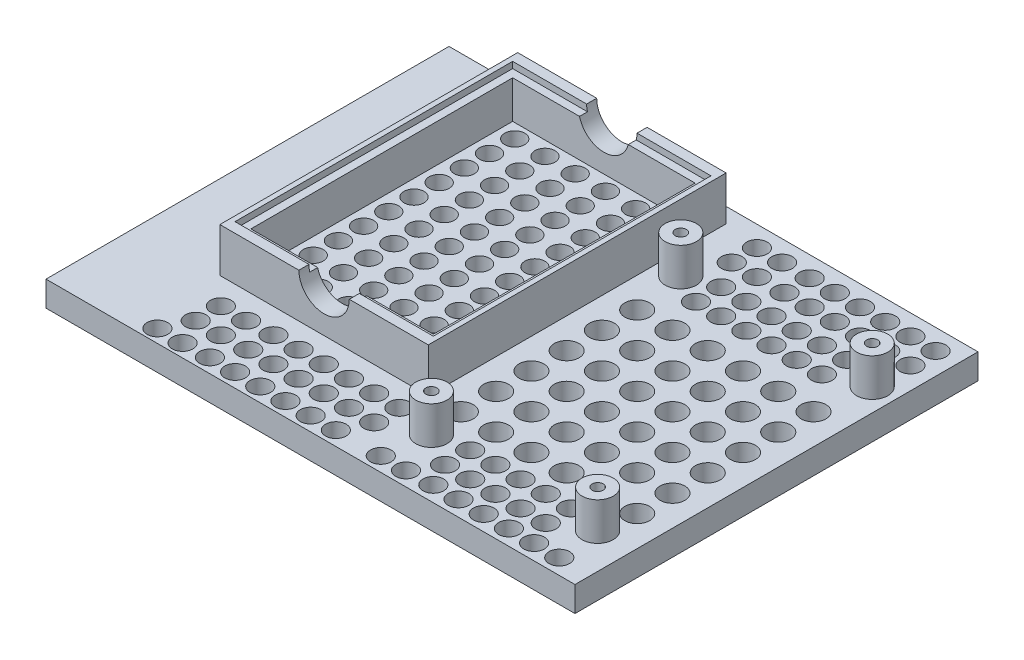
SolidWorks part; units mm, degrees
ref_plane "Front Plane" through (0, 0, 0) normal (0, 0, 1) x (1, 0, 0)
ref_plane "Top Plane" through (0, 0, 0) normal (0, 1, 0) x (1, 0, 0)
ref_plane "Right Plane" through (0, 0, 0) normal (1, 0, 0) x (0, 0, -1)
sketch "Sketch1" plane through (0, 0, 0) normal (0, 1, 0) x (1, 0, 0)
  circle A0 centre (0, 0) radius 41.275
  dimension "D1" = 82.55
extrude "Boss-Extrude1" add sketch "Sketch1" along normal blind 9.525
sketch "Sketch2" plane through (0, 0, 0) normal (0, -1, 0) x (1, 0, 0)
  line L1 (-25.4, 28.575) -> (25.4, 28.575)
  line L2 (-25.4, 28.575) -> (-25.4, 41.275)
  line L3 (-25.4, 41.275) -> (25.4, 41.275)
  line L4 (25.4, 28.575) -> (25.4, 41.275)
  line L5 (0, 41.275) -> (0, 28.575) construction
  line L6 (-25.4, 34.925) -> (25.4, 34.925) construction
  circle A0 centre (0, 0) radius 41.275 construction
  point P0 (0, 34.925)
  dimension "D1" = 12.7
  dimension "D2" = 50.8
extrude "Boss-Extrude2" add sketch "Sketch2" along normal blind 76.2
sketch "Sketch3" plane through (25.4, 0, 0) normal (1, 0, 0) x (0, 0, -1)
  line L0 (-41.275, 0) -> (-41.275, -76.2)
  line L1 (-41.275, -76.2) -> (-41.275, 0) construction
  line L2 (-41.275, -76.2) -> (-76.7393, -23.727)
  line L3 (-41.275, -76.2) -> (-28.575, -76.2) construction
  line L4 (-64.1375, 0) -> (-41.275, 0)
  line L6 (-41.275, 0) -> (-32.5341, 0) construction
  circle A0 centre (-64.1375, -15.21) radius 15.21 construction
  arc A1 (-64.1375, 0) -> (-76.7393, -23.727) centre (-64.1375, -15.21) ccw
  circle A2 centre (-64.1375, -15.21) radius 2.51
  dimension "D3" = 5.02
  dimension "D2" = 12.7
  dimension "D1" = 22.8625
extrude "Boss-Extrude3" add sketch "Sketch3" against normal blind 6.35
ref_plane "Plane1" through (7.4803, 0, 0) normal (-1, 0, 0) x (0, 0, 1)
ref_plane "Plane2" through (13.2651, 0, 0) normal (-1, 0, 0) x (0, 0, 1)
mirror "Mirror1" about plane through (13.2651, 0, 0) normal (-1, 0, 0) of "Boss-Extrude3"
sketch "Sketch5" plane through (1.1303, 0, 0) normal (-1, 0, 0) x (0, 0, 1)
  line L0 (42.9875, 0) -> (42.9875, 5.94)
  line L1 (42.9875, -36.36) -> (85.2875, -36.36) construction
  line L2 (42.9875, -36.36) -> (42.9875, 5.94) construction
  line L3 (42.9875, 5.94) -> (85.2875, 5.94) construction
  line L4 (85.2875, -36.36) -> (85.2875, 5.94) construction
  line L5 (64.1375, 5.94) -> (64.1375, -36.36) construction
  line L6 (42.9875, -15.21) -> (85.2875, -15.21) construction
  line L7 (41.275, 0) -> (64.1375, 0) construction
  line L8 (42.9875, 5.94) -> (85.2875, 5.94)
  line L9 (85.2875, 5.94) -> (85.2875, -36.36)
  line L10 (85.2875, -36.36) -> (68.2012, -36.36)
  line L11 (76.7393, -23.727) -> (41.275, -76.2) construction
  line L12 (64.1375, 0) -> (42.9875, 0)
  line L13 (76.7393, -23.727) -> (68.2012, -36.36)
  arc A0 (64.1375, 0) -> (76.7393, -23.727) centre (64.1375, -15.21) cw
  arc A1 (76.7393, -23.727) -> (64.1375, 0) centre (64.1375, -15.21) ccw construction
  point P0 (64.1375, -15.21)
  dimension "D1" = 42.3
extrude "Boss-Extrude4" add sketch "Sketch5" against normal up to surface (6.35 mm away) up to face at (7.4803, -24.0348, 57.6397)
sketch "Sketch6" plane through (1.1303, 0, 0) normal (-1, 0, 0) x (0, 0, 1)
  line L1 (48.6375, -30.71) -> (79.6375, -30.71) construction
  line L2 (48.6375, -30.71) -> (48.6375, 0.29) construction
  line L3 (48.6375, 0.29) -> (79.6375, 0.29) construction
  line L4 (79.6375, -30.71) -> (79.6375, 0.29) construction
  line L5 (64.1375, 0.29) -> (64.1375, -30.71) construction
  line L6 (48.6375, -15.21) -> (79.6375, -15.21) construction
  circle A0 centre (48.6375, 0.29) radius 2
  circle A1 centre (79.6375, 0.29) radius 2
  circle A2 centre (79.6375, -30.71) radius 2
  circle A3 centre (48.6375, -30.71) radius 2
  point P0 (64.1375, -15.21)
  dimension "D2" = 4
  dimension "D1" = 31
extrude "Cut-Extrude1" cut sketch "Sketch6" against normal through all
sketch "Sketch7" plane through (1.1303, 0, 0) normal (-1, 0, 0) x (0, 0, 1)
  circle A0 centre (64.1375, -15.21) radius 10.9995
  dimension "D1" = 21.9989
extrude "Cut-Extrude2" cut sketch "Sketch7" against normal blind 2.0015
sketch "Sketch8" plane through (25.4, 0, 0) normal (-1, 0, 0) x (0, 0, 1)
  line L1 (55.1485, -74.46) -> (61.7525, -74.46)
  line L2 (55.1485, -74.46) -> (55.1485, -36.36)
  line L3 (55.1485, -36.36) -> (61.7525, -36.36)
  line L4 (61.7525, -74.46) -> (61.7525, -36.36)
  line L5 (58.4505, -36.36) -> (58.4505, -74.46) construction
  line L6 (55.1485, -55.41) -> (61.7525, -55.41) construction
  line L7 (68.2012, -36.36) -> (85.2875, -36.36) construction
  line L8 (41.275, -76.2) -> (41.275, 0) construction
  point P220 (58.4505, -55.41)
  dimension "D1" = 13.8735
  dimension "D2" = 6.604
  dimension "D3" = 38.1
extrude "Boss-Extrude5" add sketch "Sketch8" along normal up to surface (24.2697 mm away)
sketch "Sketch9" plane through (0, 9.525, 0) normal (0, 1, 0) x (1, 0, 0)
  line L1 (17.6771, -17.6771) -> (-17.6771, -17.6771) construction
  line L2 (17.6771, -17.6771) -> (17.6771, 17.6771) construction
  line L3 (17.6771, 17.6771) -> (-17.6771, 17.6771) construction
  line L4 (-17.6771, -17.6771) -> (-17.6771, 17.6771) construction
  line L5 (0, 17.6771) -> (0, -17.6771) construction
  line L6 (17.6771, 0) -> (-17.6771, 0) construction
  circle A0 centre (-17.6771, -17.6771) radius 2.5006
  circle A1 centre (17.6771, -17.6771) radius 2.5006
  circle A2 centre (17.6771, 17.6771) radius 2.5006
  circle A3 centre (-17.6771, 17.6771) radius 2.5006
  point P0 (0, 0)
  dimension "D2" = 5.0013
  dimension "D1" = 35.3543
extrude "Cut-Extrude3" cut sketch "Sketch9" against normal through all
sketch "Sketch11" plane through (0, 0, 0) normal (1, 0, 0) x (0, 0, -1)
  line L0 (34.925, 0) -> (-28.575, -76.2)
  line L1 (-32.5341, 0) -> (41.275, 0) construction
  dimension "D1" = 6.35
rib "Rib2" sketch "Sketch11" sketch "Sketch11" thickness 12.7 extrusion direction parallel to sketch draft on no parameters "D1"=12.7
fillet "Fillet2" radius 6.35 3 edges at (-6.35, -38.1, 28.575) (6.35, -38.1, 28.575) (0, 0, -41.275)
fillet "Fillet3" radius 6.35 6 edges at (-19.05, -76.2, 28.575) (-8.2099, -73.9682, 26.7151) (19.05, -76.2, 28.575) (8.2099, -73.9682, 26.7151) (-6.35, -34.276, -6.3617) (6.35, -34.276, -6.3617)
fillet "Fillet4" radius 6.35 9 edges at (-6.6806, -73.6896, 26.9338) (6.6687, -73.7059, 26.9387) (0, -76.2, 28.575) (-25.4, -76.2, 38.1) (-25.4, -74.3401, 30.4349) (25.4, -76.2, 38.1) (25.4, -74.3401, 30.4349) (-25.4, -34.4604, 28.575) (25.4, -34.4604, 28.575)
fillet "Fillet5" radius 2.032 12 edges at (4.3053, -45.9015, 61.7525) (22.225, -45.9015, 61.7525) (1.1303, -74.46, 58.4505) (13.2651, -74.46, 55.1485) (25.4, -74.46, 58.4505) (0.5651, 0, 41.275) (1.1303, 0, 42.1313) (4.3053, 5.94, 85.2875) (4.3053, -36.36, 85.2875) (4.3053, -36.36, 68.2012) (4.3053, 0, 42.9875) (4.3053, 5.94, 42.9875)
sketch "Sketch12" plane through (0, 0, 0) normal (0, 1, 0) x (1, 0, 0)
  line L0 (25.4, -34.925) -> (25.4, -46.6587) construction
  line L1 (25.4, -32.5341) -> (158.75, -32.5341)
  line L2 (25.4, -32.5341) -> (25.4, 69.0659)
  line L3 (25.4, 69.0659) -> (158.75, 69.0659)
  line L4 (158.75, -32.5341) -> (158.75, 69.0659)
  line L5 (92.075, 69.0659) -> (92.075, -32.5341) construction
  line L6 (25.4, 18.2659) -> (158.75, 18.2659) construction
  circle A0 centre (0, 0) radius 41.275 construction
  point P288 (92.075, 18.2659)
  dimension "D1" = 101.6
  dimension "D2" = 133.35
extrude "Boss-Extrude6" add sketch "Sketch12" against normal blind 6.35
sketch "Sketch13" plane through (0, 0, 0) normal (0, 1, 0) x (1, 0, 0)
  line L0 (158.75, -32.5341) -> (158.75, 69.0659) construction
  line L1 (156.21, -26.1841) -> (156.21, 62.7159) construction
  line L2 (156.21, -26.1841) -> (101.6, -26.1841) construction
  line L3 (101.6, -26.1841) -> (101.6, 62.7159) construction
  line L4 (156.21, 62.7159) -> (101.6, 62.7159) construction
  line L5 (101.6, 18.2659) -> (156.21, 18.2659) construction
  line L6 (128.905, -26.1841) -> (128.905, 62.7159) construction
  line L7 (47.79, -7.2841) -> (97.79, -7.2841)
  line L8 (47.79, -7.2841) -> (47.79, 62.7159)
  line L9 (47.79, 62.7159) -> (97.79, 62.7159)
  line L10 (97.79, -7.2841) -> (97.79, 62.7159)
  line L11 (72.79, 62.7159) -> (72.79, -7.2841) construction
  line L12 (47.79, 27.7159) -> (97.79, 27.7159) construction
  line L13 (25.4, -32.5341) -> (158.75, -32.5341) construction
  line L15 (95.79, -5.2841) -> (49.79, -5.2841)
  line L16 (95.79, -5.2841) -> (95.79, 60.7159)
  line L17 (95.79, 60.7159) -> (49.79, 60.7159)
  line L18 (49.79, -5.2841) -> (49.79, 60.7159)
  line L19 (72.79, 60.7159) -> (72.79, -5.2841) construction
  line L20 (95.79, 27.7159) -> (49.79, 27.7159) construction
  circle A0 centre (107.95, -17.9291) radius 1.397
  circle A1 centre (104.775, 48.1109) radius 1.397
  circle A2 centre (0, 0) radius 41.275 construction
  circle A3 centre (149.86, -17.9291) radius 1.397
  circle A4 centre (153.035, 48.1109) radius 1.397
  circle A5 centre (0, 0) radius 41.275 construction
  circle A6 centre (104.775, 48.1109) radius 3.937
  circle A7 centre (153.035, 48.1109) radius 3.937
  circle A8 centre (107.95, -17.9291) radius 3.937
  circle A9 centre (149.86, -17.9291) radius 3.937
  point P0 (128.905, 18.2659)
  point P5 (72.79, 27.7159)
  point P20 (72.79, 27.7159)
  dimension "D5" = 6.35
  dimension "D6" = 8.255
  dimension "D7" = 3.175
  dimension "D8" = 14.605
  dimension "D9" = 2.794
  dimension "D15" = 2.54
  dimension "D1" = 54.61
  dimension "D2" = 88.9
  dimension "D3" = 50
  dimension "D4" = 70
  dimension "D10" = 2.54
  dimension "D11" = 50.8
  dimension "D12" = 3.81
  dimension "D13" = 2
  dimension "D14" = 2
extrude "Boss-Extrude7" add sketch "Sketch13" along normal blind 9.525
sketch "Sketch14" plane through (0, 0, 0) normal (0, 1, 0) x (1, 0, 0)
  line L0 (97.79, 62.7159) -> (47.79, 62.7159) construction
  line L1 (46.52, 65.2559) -> (99.06, 65.2559)
  line L2 (46.52, 65.2559) -> (46.52, -9.8241)
  line L3 (46.52, -9.8241) -> (99.06, -9.8241)
  line L4 (99.06, 65.2559) -> (99.06, -9.8241)
  line L5 (72.79, -9.8241) -> (72.79, 65.2559) construction
  line L6 (46.52, 27.7159) -> (99.06, 27.7159) construction
  line L7 (97.79, -7.2841) -> (97.79, 62.7159) construction
  line L8 (97.79, 62.7159) -> (47.79, 62.7159) construction
  line L9 (47.79, 62.7159) -> (47.79, -7.2841) construction
  line L11 (47.79, 62.7159) -> (97.79, 62.7159)
  line L12 (47.79, 62.7159) -> (47.79, -7.2841)
  line L13 (47.79, -7.2841) -> (97.79, -7.2841)
  line L14 (97.79, 62.7159) -> (97.79, -7.2841)
  line L15 (72.79, -7.2841) -> (72.79, 62.7159) construction
  line L16 (47.79, 27.7159) -> (97.79, 27.7159) construction
  point P8 (72.79, 62.7159)
  point P12 (47.79, 27.7159)
  point P200 (72.79, 27.7159)
  point P423 (72.79, 27.7159)
  dimension "D1" = 2.54
  dimension "D2" = 1.27
extrude "Boss-Extrude8" add sketch "Sketch14" along normal offset from surface (11.1125 mm away) 1.5875
sketch "Sketch15" plane through (0, 0, 9.8241) normal (0, 0, 1) x (1, 0, 0)
  line L0 (99.06, 11.1125) -> (46.52, 11.1125) construction
  line L1 (66.44, 11.1125) -> (79.14, 11.1125)
  arc A0 (66.44, 11.1125) -> (79.14, 11.1125) centre (72.79, 11.1125) ccw
  dimension "D1" = 12.7
extrude "Cut-Extrude4" cut sketch "Sketch15" against normal through all
sketch "Sketch16" plane through (0, 9.525, 0) normal (0, 1, 0) x (1, 0, 0)
  circle A0 centre (0, 0) radius 41.275
  circle A1 centre (-17.6771, 17.6771) radius 2.5006
  circle A2 centre (17.6771, 17.6771) radius 2.5006
  circle A3 centre (17.6771, -17.6771) radius 2.5006
  circle A4 centre (-17.6771, -17.6771) radius 2.5006
  circle A5 centre (0, 0) radius 41.275 construction
  circle A6 centre (-17.6771, -17.6771) radius 2.5006 construction
extrude "Boss-Extrude9" add sketch "Sketch16" along normal up to surface (1.5875 mm away)
sketch "Sketch17" plane through (7.4803, 0, 0) normal (1, 0, 0) x (0, 0, -1)
  circle A0 centre (-48.6375, 0.29) radius 2.9997
  circle A1 centre (-79.6375, 0.29) radius 2.9997
  circle A2 centre (-48.6375, -30.71) radius 2.9997
  circle A3 centre (-79.1747, -30.9662) radius 2.9997
  dimension "D1" = 5.9995
extrude "Cut-Extrude5" cut sketch "Sketch17" against normal blind 4.0005
sketch "Sketch18" plane through (1.1303, 0, 0) normal (-1, 0, 0) x (0, 0, 1)
  line L0 (83.2555, 5.94) -> (45.0195, 5.94) construction
  line L1 (83.2555, -36.36) -> (45.0195, -36.36)
  line L2 (85.2875, -34.328) -> (85.2875, 3.908)
  line L3 (83.2555, 5.94) -> (45.0195, 5.94)
  line L4 (42.9875, -34.328) -> (42.9875, 3.908)
  line L5 (64.1375, 5.94) -> (64.1375, -36.36) construction
  line L6 (85.2875, -15.21) -> (42.9875, -15.21) construction
  line L7 (42.9875, 3.908) -> (42.9875, 2.032) construction
  arc A0 (45.0195, -36.36) -> (42.9875, -34.328) centre (45.0195, -34.328) cw
  arc A1 (83.2555, -36.36) -> (85.2875, -34.328) centre (83.2555, -34.328) ccw
  arc A2 (85.2875, 3.908) -> (83.2555, 5.94) centre (83.2555, 3.908) ccw
  arc A3 (45.0195, 5.94) -> (42.9875, 3.908) centre (45.0195, 3.908) ccw
  circle A4 centre (48.6375, 0.29) radius 2
  circle A5 centre (48.6375, 0.29) radius 2 construction
  circle A6 centre (48.6375, -30.71) radius 2
  circle A7 centre (79.6375, 0.29) radius 2
  circle A8 centre (79.6375, -30.71) radius 2
  circle A9 centre (64.1375, -15.21) radius 10.9995
  circle A10 centre (64.1375, -15.21) radius 10.9995 construction
  point P0 (64.1375, -15.21)
  dimension "D1" = 2.032
extrude "Boss-Extrude10" add sketch "Sketch18" along normal blind 2.6492
sketch "Sketch19" plane through (0, 0, -69.0659) normal (0, 0, -1) x (-1, 0, 0)
  line L0 (-41.275, 11.1125) -> (-41.275, 0)
  line L1 (-158.75, 0) -> (-25.4, 0) construction
  line L2 (-41.275, 0) -> (-25.4, 0)
  line L3 (-25.4, -6.35) -> (-25.4, 0) construction
  line L4 (-25.4, 0) -> (-25.4, -76.2)
  line L5 (-25.4, -76.2) -> (25.9886, -76.2)
  line L6 (25.9886, -76.2) -> (25.9886, 0)
  line L8 (25.9886, 0) -> (41.275, 0)
  line L9 (41.275, 0) -> (41.275, 11.1125)
  line L10 (41.275, 11.1125) -> (-41.275, 11.1125)
  line L11 (4.0774, -76.2) -> (-4.0774, -76.2) construction
  line L12 (0, 0) -> (34.925, 0) construction
extrude "Cut-Extrude6" cut sketch "Sketch19" against normal through all
sketch "Sketch20" plane through (0, 0, 0) normal (0, 1, 0) x (1, 0, 0)
  line L0 (95.79, -5.2841) -> (95.79, 60.7159) construction
  line L1 (158.75, -32.5341) -> (158.75, 69.0659) construction
  line L2 (158.75, 18.2659) -> (25.4, 18.2659) construction
  line L3 (25.4, 69.0659) -> (25.4, -32.5341) construction
  circle A0 centre (91.98, 0) radius 2.5244
  circle A1 centre (84.36, 0) radius 2.5244
  circle A2 centre (76.74, 0) radius 2.5244
  circle A3 centre (69.12, 0) radius 2.5244
  circle A4 centre (61.5, 0) radius 2.5244
  circle A5 centre (53.88, 0) radius 2.5244
  circle A6 centre (91.98, 6.35) radius 2.5244
  circle A7 centre (84.36, 6.35) radius 2.5244
  circle A8 centre (53.88, 6.35) radius 2.5244
  circle A9 centre (69.12, 6.35) radius 2.5244
  circle A10 centre (76.74, 6.35) radius 2.5244
  circle A11 centre (61.5, 6.35) radius 2.5244
  circle A12 centre (91.98, 12.7) radius 2.5244
  circle A13 centre (84.36, 12.7) radius 2.5244
  circle A14 centre (53.88, 12.7) radius 2.5244
  circle A15 centre (69.12, 12.7) radius 2.5244
  circle A16 centre (76.74, 12.7) radius 2.5244
  circle A17 centre (61.5, 12.7) radius 2.5244
  circle A18 centre (91.98, 19.05) radius 2.5244
  circle A19 centre (84.36, 19.05) radius 2.5244
  circle A20 centre (53.88, 19.05) radius 2.5244
  circle A21 centre (69.12, 19.05) radius 2.5244
  circle A22 centre (76.74, 19.05) radius 2.5244
  circle A23 centre (61.5, 19.05) radius 2.5244
  circle A24 centre (91.98, 25.4) radius 2.5244
  circle A25 centre (84.36, 25.4) radius 2.5244
  circle A26 centre (53.88, 25.4) radius 2.5244
  circle A27 centre (69.12, 25.4) radius 2.5244
  circle A28 centre (76.74, 25.4) radius 2.5244
  circle A29 centre (61.5, 25.4) radius 2.5244
  circle A30 centre (91.98, 31.75) radius 2.5244
  circle A31 centre (84.36, 31.75) radius 2.5244
  circle A32 centre (53.88, 31.75) radius 2.5244
  circle A33 centre (69.12, 31.75) radius 2.5244
  circle A34 centre (76.74, 31.75) radius 2.5244
  circle A35 centre (61.5, 31.75) radius 2.5244
  circle A36 centre (91.98, 38.1) radius 2.5244
  circle A37 centre (84.36, 38.1) radius 2.5244
  circle A38 centre (53.88, 38.1) radius 2.5244
  circle A39 centre (69.12, 38.1) radius 2.5244
  circle A40 centre (76.74, 38.1) radius 2.5244
  circle A41 centre (61.5, 38.1) radius 2.5244
  circle A42 centre (91.98, 44.45) radius 2.5244
  circle A43 centre (84.36, 44.45) radius 2.5244
  circle A44 centre (53.88, 44.45) radius 2.5244
  circle A45 centre (69.12, 44.45) radius 2.5244
  circle A46 centre (76.74, 44.45) radius 2.5244
  circle A47 centre (61.5, 44.45) radius 2.5244
  circle A48 centre (91.98, 50.8) radius 2.5244
  circle A49 centre (84.36, 50.8) radius 2.5244
  circle A50 centre (53.88, 50.8) radius 2.5244
  circle A51 centre (69.12, 50.8) radius 2.5244
  circle A52 centre (76.74, 50.8) radius 2.5244
  circle A53 centre (61.5, 50.8) radius 2.5244
  circle A54 centre (91.98, 57.15) radius 2.5244
  circle A55 centre (84.36, 57.15) radius 2.5244
  circle A56 centre (53.88, 57.15) radius 2.5244
  circle A57 centre (69.12, 57.15) radius 2.5244
  circle A58 centre (76.74, 57.15) radius 2.5244
  circle A59 centre (61.5, 57.15) radius 2.5244
  circle A60 centre (151.1007, -9.1992) radius 3.1326
  circle A61 centre (141.6398, -16.4383) radius 2.6018
  circle A62 centre (144.018, 50.8) radius 2.6018
  circle A63 centre (137.668, 50.8) radius 2.6018
  circle A64 centre (131.318, 50.8) radius 2.6018
  circle A65 centre (124.968, 50.8) radius 2.6018
  circle A66 centre (118.618, 50.8) radius 2.6018
  circle A67 centre (112.268, 50.8) radius 2.6018
  circle A68 centre (137.668, 44.45) radius 2.6018
  circle A69 centre (131.318, 44.45) radius 2.6018
  circle A70 centre (124.968, 44.45) radius 2.6018
  circle A71 centre (118.618, 44.45) radius 2.6018
  circle A72 centre (112.268, 44.45) radius 2.6018
  circle A73 centre (144.018, 44.45) radius 2.6018
  circle A74 centre (142.2107, -9.1992) radius 3.1326
  circle A75 centre (133.3207, -9.1992) radius 3.1326
  circle A76 centre (124.4307, -9.1992) radius 3.1326
  circle A77 centre (115.5407, -9.1992) radius 3.1326
  circle A78 centre (106.6507, -9.1992) radius 3.1326
  circle A79 centre (142.2107, -0.3092) radius 3.1326
  circle A80 centre (133.3207, -0.3092) radius 3.1326
  circle A81 centre (124.4307, -0.3092) radius 3.1326
  circle A82 centre (115.5407, -0.3092) radius 3.1326
  circle A83 centre (106.6507, -0.3092) radius 3.1326
  circle A84 centre (142.2107, 8.5808) radius 3.1326
  circle A85 centre (133.3207, 8.5808) radius 3.1326
  circle A86 centre (124.4307, 8.5808) radius 3.1326
  circle A87 centre (115.5407, 8.5808) radius 3.1326
  circle A88 centre (106.6507, 8.5808) radius 3.1326
  circle A89 centre (142.2107, 17.4708) radius 3.1326
  circle A90 centre (133.3207, 17.4708) radius 3.1326
  circle A91 centre (124.4307, 17.4708) radius 3.1326
  circle A92 centre (115.5407, 17.4708) radius 3.1326
  circle A93 centre (106.6507, 17.4708) radius 3.1326
  circle A94 centre (142.2107, 26.3608) radius 3.1326
  circle A95 centre (133.3207, 26.3608) radius 3.1326
  circle A96 centre (124.4307, 26.3608) radius 3.1326
  circle A97 centre (115.5407, 26.3608) radius 3.1326
  circle A98 centre (106.6507, 26.3608) radius 3.1326
  circle A99 centre (142.2107, 35.2508) radius 3.1326
  circle A100 centre (133.3207, 35.2508) radius 3.1326
  circle A101 centre (124.4307, 35.2508) radius 3.1326
  circle A102 centre (115.5407, 35.2508) radius 3.1326
  circle A103 centre (106.6507, 35.2508) radius 3.1326
  circle A104 centre (151.1007, -0.3092) radius 3.1326
  circle A105 centre (151.1007, 8.5808) radius 3.1326
  circle A106 centre (151.1007, 17.4708) radius 3.1326
  circle A107 centre (151.1007, 26.3608) radius 3.1326
  circle A108 centre (151.1007, 35.2508) radius 3.1326
  circle A109 centre (135.2898, -16.4383) radius 2.6018
  circle A110 centre (128.9398, -16.4383) radius 2.6018
  circle A111 centre (122.5898, -16.4383) radius 2.6018
  circle A112 centre (116.2398, -16.4383) radius 2.6018
  circle A113 centre (153.2189, 63.9054) radius 2.6018
  circle A114 centre (135.2898, -22.7883) radius 2.6018
  circle A115 centre (128.9398, -22.7883) radius 2.6018
  circle A116 centre (122.5898, -22.7883) radius 2.6018
  circle A117 centre (116.2398, -22.7883) radius 2.6018
  circle A118 centre (146.8689, 63.9054) radius 2.6018
  circle A119 centre (141.6398, -22.7883) radius 2.6018
  circle A120 centre (140.5189, 63.9054) radius 2.6018
  circle A121 centre (134.1689, 63.9054) radius 2.6018
  circle A122 centre (127.8189, 63.9054) radius 2.6018
  circle A123 centre (121.4689, 63.9054) radius 2.6018
  circle A124 centre (146.8689, 57.5554) radius 2.6018
  circle A125 centre (140.5189, 57.5554) radius 2.6018
  circle A126 centre (134.1689, 57.5554) radius 2.6018
  circle A127 centre (127.8189, 57.5554) radius 2.6018
  circle A128 centre (121.4689, 57.5554) radius 2.6018
  circle A129 centre (153.2189, 57.5554) radius 2.6018
  circle A130 centre (114.5686, 63.8666) radius 2.6018
  circle A131 centre (108.2186, 63.8666) radius 2.6018
  circle A132 centre (98.0525, -16.1079) radius 2.6018
  circle A133 centre (91.7025, -16.1079) radius 2.6018
  circle A134 centre (85.3525, -16.1079) radius 2.6018
  circle A135 centre (79.0025, -16.1079) radius 2.6018
  circle A136 centre (108.2186, 57.5166) radius 2.6018
  circle A137 centre (72.6525, -16.1079) radius 2.6018
  circle A138 centre (66.3025, -16.1079) radius 2.6018
  circle A139 centre (91.7025, -22.4579) radius 2.6018
  circle A140 centre (85.3525, -22.4579) radius 2.6018
  circle A141 centre (114.5686, 57.5166) radius 2.6018
  circle A142 centre (79.0025, -22.4579) radius 2.6018
  circle A143 centre (72.6525, -22.4579) radius 2.6018
  circle A144 centre (66.3025, -22.4579) radius 2.6018
  circle A145 centre (98.0525, -22.4579) radius 2.6018
  circle A146 centre (59.7081, -16.4043) radius 2.6018
  circle A147 centre (53.3581, -16.4043) radius 2.6018
  circle A148 centre (144.544, -28.6379) radius 2.6018
  circle A149 centre (138.194, -28.6379) radius 2.6018
  circle A150 centre (131.844, -28.6379) radius 2.6018
  circle A151 centre (125.494, -28.6379) radius 2.6018
  circle A152 centre (53.3581, -22.7543) radius 2.6018
  circle A153 centre (119.144, -28.6379) radius 2.6018
  circle A154 centre (150.894, -28.6379) radius 2.6018
  circle A155 centre (106.1996, -28.9343) radius 2.6018
  circle A156 centre (112.5496, -28.9343) radius 2.6018
  circle A157 centre (59.7081, -22.7543) radius 2.6018
  circle A158 centre (88.5553, -28.9736) radius 2.6018
  circle A159 centre (82.2053, -28.9736) radius 2.6018
  circle A160 centre (75.8553, -28.9736) radius 2.6018
  circle A161 centre (69.5053, -28.9736) radius 2.6018
  circle A162 centre (63.1553, -28.9736) radius 2.6018
  circle A163 centre (94.9053, -28.9736) radius 2.6018
  circle A164 centre (50.2109, -29.2701) radius 2.6018
  circle A165 centre (56.5609, -29.2701) radius 2.6018
  point P272 (0, 0)
  dimension "D2" = 3.81
  dimension "D6" = 14.732
  dimension "D1" = 6
  dimension "D3" = 10
  dimension "D4" = 6
  dimension "D5" = 2
  dimension "D7" = 6
  dimension "D8" = 6
extrude "Cut-Extrude7" cut sketch "Sketch20" against normal through all
